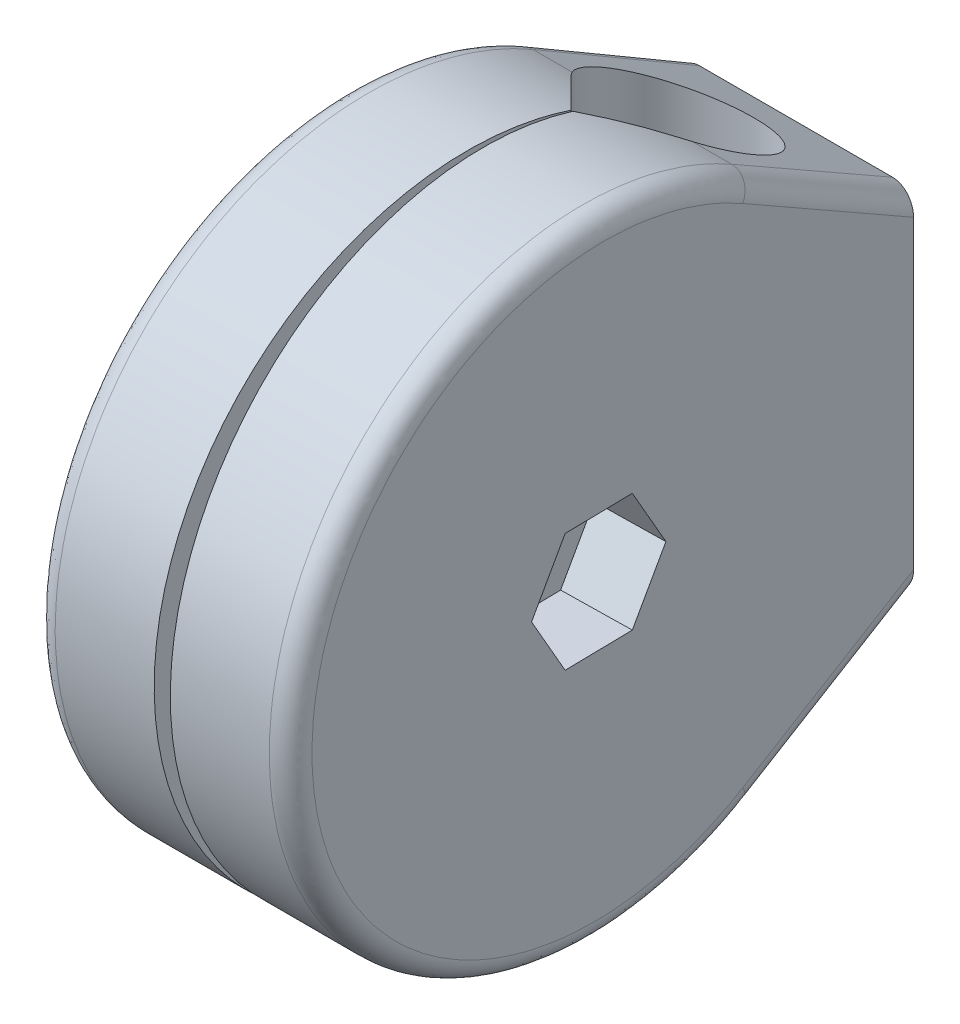
SolidWorks part; units mm, degrees
material "PETG"
ref_plane "Front Plane" through (0, 0, 0) normal (0, 0, 1) x (1, 0, 0)
ref_plane "Top Plane" through (0, 0, 0) normal (0, 1, 0) x (1, 0, 0)
ref_plane "Right Plane" through (0, 0, 0) normal (1, 0, 0) x (0, 0, -1)
sketch "Sketch1" plane through (0, 0, 0) normal (1, 0, 0) x (0, 0, -1)
  line L0 (22.225, 38.4948) -> (45.45, 25.0859)
  line L1 (45.45, 25.0859) -> (45.45, -25.0859)
  line L2 (45.45, -25.0859) -> (22.225, -38.4948)
  line L3 (36.6947, 25.0859) -> (45.45, 25.0859) construction
  circle A0 centre (0, 0) radius 44.45 construction
  arc A1 (22.225, 38.4948) -> (22.225, -38.4948) centre (0, 0) ccw
  point P9 (44.45, 0)
  dimension "D3" = 88.9
  dimension "D1" = 150
  dimension "D2" = 120
  dimension "D4" = 1
extrude "Boss-Extrude1" add sketch "Sketch1" along normal mid plane 33.336
sketch "Sketch2" plane through (0, 0, 0) normal (0, 1, 0) x (1, 0, 0)
  line L0 (-7.5883, 21.1302) -> (0, 13.8022) construction
  line L1 (16.668, 45.45) -> (-16.668, 45.45) construction
  line L2 (0, 13.8022) -> (0, -44.45) construction
  line L3 (-7.5883, 21.1302) -> (-0.129, 13.6709)
  line L4 (7.5883, 21.1302) -> (0.129, 13.6709)
  line L5 (-0.129, 13.6709) -> (-1.1436, -44.45)
  line L6 (-16.668, -44.45) -> (16.668, -44.45) construction
  line L7 (0.129, 13.6709) -> (1.1436, -44.45)
  line L8 (1.1436, -44.45) -> (-1.1436, -44.45)
  line L9 (7.5883, 21.1302) -> (0, 13.8022) construction
  arc A0 (7.5883, 21.1302) -> (-7.5883, 21.1302) centre (0, 28.7185) ccw
  arc A1 (-0.129, 13.6709) -> (0, 13.8022) centre (-7.5883, 21.1302) ccw construction
  point P6 (-10.7315, 28.7185)
  point P8 (0, 39.45)
  point P9 (10.7315, 28.7185)
  dimension "D1" = 10.7315
  dimension "D3" = 90
  dimension "D2" = 6
  dimension "D4" = 2
  dimension "D5" = 1
extrude "Cut-Extrude1" cut sketch "Sketch2" against normal through all both and the other way through all
draft "Draft1" type of draft neutral plane draft angle 1 faces to draft 2 face at (16.668, 0, -17.1688) face at (-16.668, 0, -17.1688) neutral plane through (16.668, 25.0859, -45.45) neutral plane normal (0, 0, -1) parameters "D1"=1
sketch "Sketch3" plane through (17.456, 0, -0.3047) normal (0.9998, 0, -0.0175) x (-0.0175, 0, -0.9998)
  circle A0 centre (-0.3047, 0) radius 5.5
  ellipse E0 centre (-0.3047, 0) end of major axis (44.152, 0) minor radius 44.45 (21.9236, 38.4948) -> (21.9236, -38.4948) ccw construction
  dimension "D1" = 11
extrude "Cut-Extrude2" cut sketch "Sketch3" against normal up to next
sketch "Sketch4" plane through (17.456, 0, -0.3047) normal (0.9998, 0, -0.0175) x (-0.0175, 0, -0.9998)
  line L1 (9.3947, 0) -> (4.545, 8.4)
  line L2 (4.545, 8.4) -> (-5.1545, 8.4)
  line L3 (-5.1545, 8.4) -> (-10.0042, 0)
  line L4 (-10.0042, 0) -> (-5.1545, -8.4)
  line L5 (-5.1545, -8.4) -> (4.545, -8.4)
  line L6 (4.545, -8.4) -> (9.3947, 0)
  circle A0 centre (-0.3047, 0) radius 8.4 construction
  dimension "D1" = 16.8
extrude "Cut-Extrude3" cut sketch "Sketch4" against normal blind 10
sketch "Sketch5" plane through (-17.456, 0, -0.3047) normal (-0.9998, 0, -0.0175) x (-0.0175, 0, 0.9998)
  circle A0 centre (0.3047, 0) radius 5.5
  ellipse E0 centre (0.3047, 0) end of major axis (44.7615, 0) minor radius 44.45 (-21.9236, -38.4948) -> (-21.9236, 38.4948) ccw construction
  dimension "D1" = 11
extrude "Cut-Extrude4" cut sketch "Sketch5" against normal up to next
fillet "Fillet1" radius 3 6 edges at (16.8707, 31.7903, -33.8375) (16.8707, -31.7903, -33.8375) (-16.8707, 31.7903, -33.8375) (-16.8707, -31.7903, -33.8375) (18.2372, 0, 44.45) (-18.2372, 0, 44.45)
sketch "Sketch6" plane through (-17.456, 0, -0.3047) normal (-0.9998, 0, -0.0175) x (-0.0175, 0, 0.9998)
  circle A0 centre (0, 0) radius 9.0394
split line "Split Line1" [suppressed]
